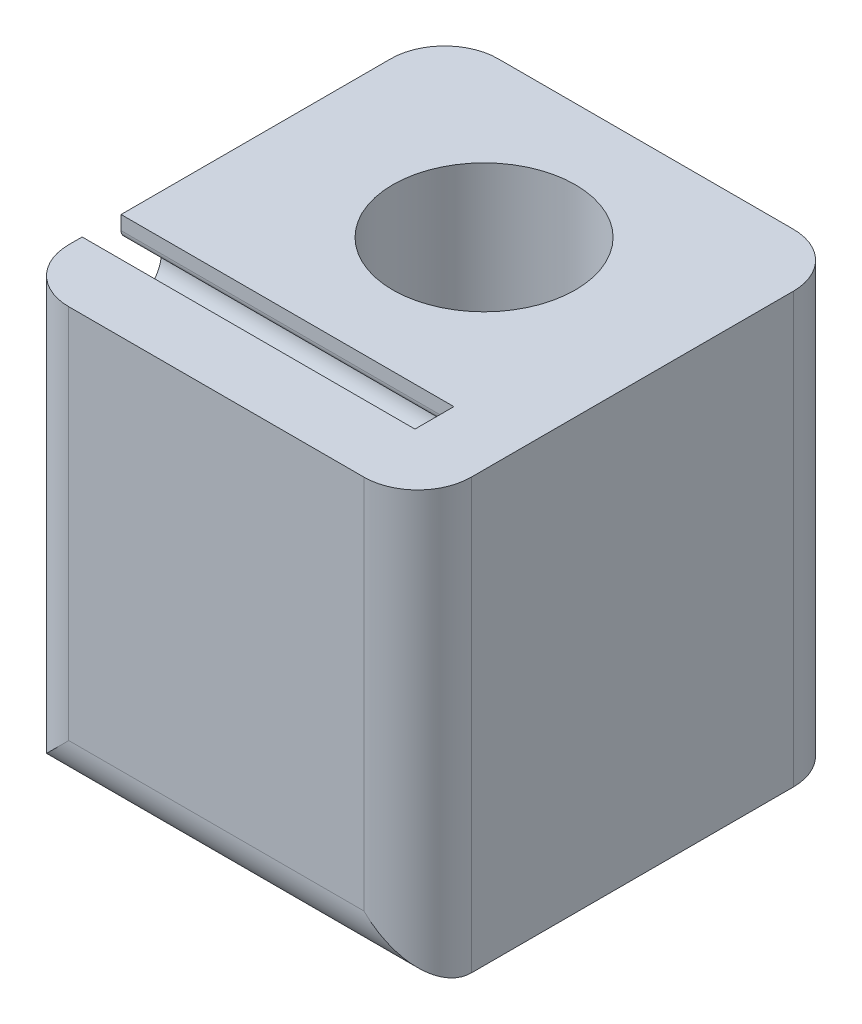
SolidWorks part; units mm, degrees
material "ABS"
ref_plane "Front Plane" through (0, 0, 0) normal (0, 0, 1) x (1, 0, 0)
ref_plane "Top Plane" through (0, 0, 0) normal (0, 1, 0) x (1, 0, 0)
ref_plane "Right Plane" through (0, 0, 0) normal (1, 0, 0) x (0, 0, -1)
sketch "Sketch1" plane through (0, 0, 0) normal (1, 0, 0) x (0, 0, -1)
  line L1 (-4, -4) -> (4, -4)
  line L2 (-4, -4) -> (-4, 4)
  line L3 (-4, 4) -> (4, 4)
  line L4 (4, -4) -> (4, 4)
  line L5 (-4, -4) -> (4, 4) construction
  line L6 (-4, 4) -> (4, -4) construction
  point P0 (0, 0)
  dimension "D1" = 8
  dimension "D2" = 8
extrude "Boss-Extrude1" add sketch "Sketch1" along normal blind 7.5
sketch "Sketch2" plane through (0, 0, 0) normal (1, 0, 0) x (0, 0, -1)
  line L0 (-2.025, 4) -> (-2.025, 3.7402)
  line L1 (4, 4) -> (-4, 4) construction
  line L2 (-1.275, 3) -> (-2.025, 3) construction
  line L4 (-2.025, 2) -> (-2.025, 2.2598)
  line L5 (-2.75, 4) -> (-2.75, -4)
  line L6 (-4, -4) -> (4, -4) construction
  line L7 (-2.025, 4) -> (-2.75, 4)
  line L8 (-4, 4) -> (-4, -4) construction
  line L9 (-2.025, 2) -> (-2.025, 1.7402)
  line L10 (-2.025, 0) -> (-2.025, 0.2598)
  line L11 (-1.275, 1) -> (-2.025, 1) construction
  line L12 (-2.025, 0) -> (-2.025, -0.2598)
  line L13 (-2.025, -2) -> (-2.025, -1.7402)
  line L14 (-1.275, -1) -> (-2.025, -1) construction
  line L15 (-2.025, -2) -> (-2.025, -2.2598)
  line L16 (-2.025, -4) -> (-2.025, -3.7402)
  line L17 (-1.275, -3) -> (-2.025, -3) construction
  line L18 (-2.025, -4) -> (-2.75, -4)
  arc A0 (-2.025, 3.7402) -> (-1.8946, 3.5915) centre (-1.875, 3.7402) ccw
  arc A1 (-1.8946, 3.5915) -> (-1.5868, 3.4989) centre (-2.025, 2.6) cw
  arc A2 (-1.5868, 3.4989) -> (-1.5868, 2.5011) centre (-1.83, 3) cw
  arc A3 (-2.025, 2.2598) -> (-1.8946, 2.4085) centre (-1.875, 2.2598) cw
  arc A4 (-1.8946, 2.4085) -> (-1.5868, 2.5011) centre (-2.025, 3.4) ccw
  arc A5 (-2.025, 1.7402) -> (-1.8946, 1.5915) centre (-1.875, 1.7402) ccw
  arc A6 (-1.8946, 1.5915) -> (-1.5868, 1.4989) centre (-2.025, 0.6) cw
  arc A7 (-1.5868, 1.4989) -> (-1.5868, 0.5011) centre (-1.83, 1) cw
  arc A8 (-2.025, 0.2598) -> (-1.8946, 0.4085) centre (-1.875, 0.2598) cw
  arc A9 (-1.8946, 0.4085) -> (-1.5868, 0.5011) centre (-2.025, 1.4) ccw
  arc A10 (-2.025, -0.2598) -> (-1.8946, -0.4085) centre (-1.875, -0.2598) ccw
  arc A11 (-1.8946, -0.4085) -> (-1.5868, -0.5011) centre (-2.025, -1.4) cw
  arc A12 (-1.5868, -0.5011) -> (-1.5868, -1.4989) centre (-1.83, -1) cw
  arc A13 (-2.025, -1.7402) -> (-1.8946, -1.5915) centre (-1.875, -1.7402) cw
  arc A14 (-1.8946, -1.5915) -> (-1.5868, -1.4989) centre (-2.025, -0.6) ccw
  arc A15 (-2.025, -2.2598) -> (-1.8946, -2.4085) centre (-1.875, -2.2598) ccw
  arc A16 (-1.8946, -2.4085) -> (-1.5868, -2.5011) centre (-2.025, -3.4) cw
  arc A17 (-1.5868, -2.5011) -> (-1.5868, -3.4989) centre (-1.83, -3) cw
  arc A18 (-2.025, -3.7402) -> (-1.8946, -3.5915) centre (-1.875, -3.7402) cw
  arc A19 (-1.8946, -3.5915) -> (-1.5868, -3.4989) centre (-2.025, -2.6) ccw
  dimension "D1" = 0.555
  dimension "D2" = 1
  dimension "D3" = 0.15
  dimension "D4" = 0.75
  dimension "D5" = 0.4
  dimension "D6" = 1
  dimension "D7" = 0.725
  dimension "D8" = 1.25
  dimension "D10" = 2
  dimension "D11" = 1.475
  dimension "D9" = 4
extrude "Cut-Extrude1" cut sketch "Sketch2" along normal blind 6.2
hole_wizard "M3 Clearance Hole1" positions "Sketch5" profile "Sketch4" hole size "M3" standard "ANSI Metric" end condition through all
sketch "Sketch5" plane through (0, 4, 0) normal (0, 1, 0) x (1, 0, 0)
  line L0 (0, 4) -> (0, -2.025) construction
  line L1 (7.5, 4) -> (0, 4) construction
  point P0 (3.75, 0.9875)
  point P9 (3.75, 4)
  point P10 (0, 0.9875)
sketch "Sketch4" plane through (3.75, 4, -0.9875) normal (1, 0, 0) x (0, 0, 1)
  line L0 (0, 0) -> (0, 8)
  line L1 (0, 8) -> (1.7, 8)
  line L2 (1.7, 8) -> (1.7, 0)
  line L5 (1.7, 0) -> (0, 0)
  line L11 (0, -6.35) -> (0, 107.95) construction
  dimension "Thru Hole Dia." = 3.4
  dimension "Thru Hole Depth" = 8
fillet "Fillet1" radius 1 5 edges at (3.75, -4, 4) (7.5, 0, 4) (7.5, 0, -4) (0, 0, -4) (0, 0, 4)
ref_plane "Plane1" through (0, 4, 0) normal (0, 1, 0) x (1, 0, 0)
